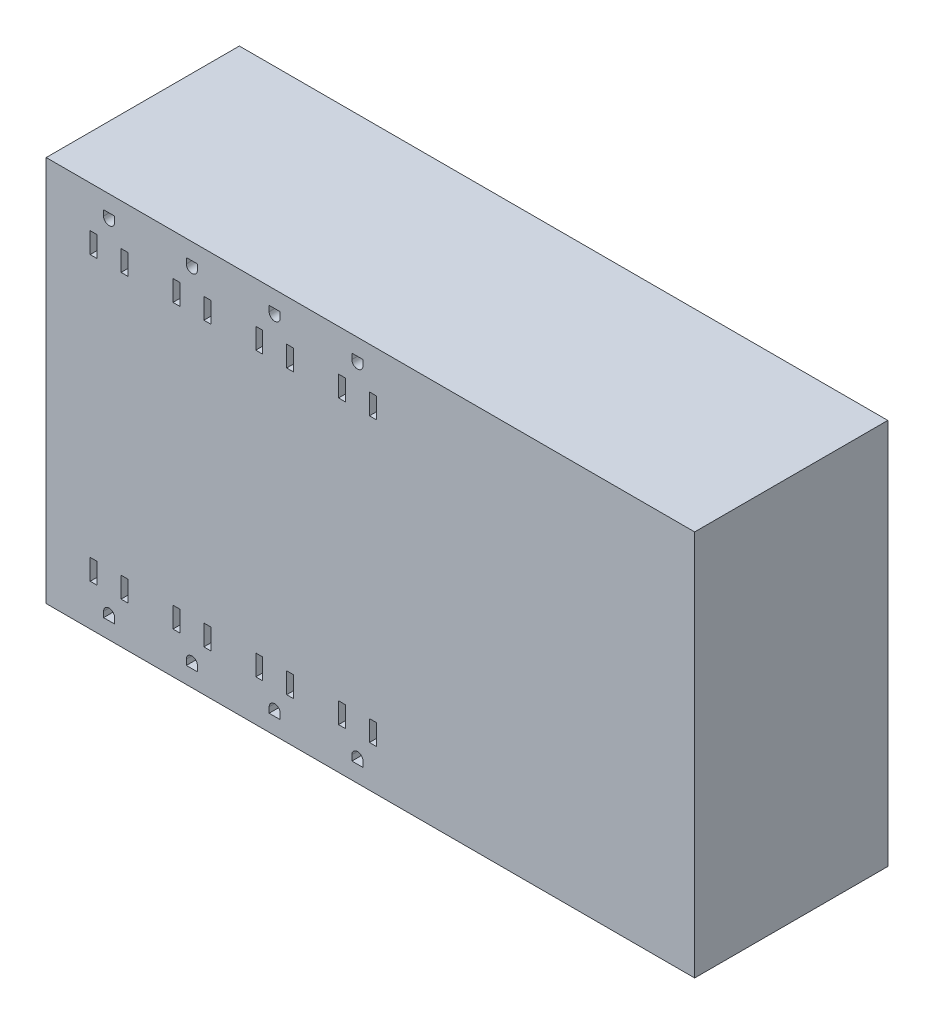
SolidWorks part; units mm, degrees
ref_plane "Front Plane" through (0, 0, 0) normal (0, 0, 1) x (1, 0, 0)
ref_plane "Top Plane" through (0, 0, 0) normal (0, 1, 0) x (1, 0, 0)
ref_plane "Right Plane" through (0, 0, 0) normal (1, 0, 0) x (0, 0, -1)
sketch "Sketch1" plane through (0, 0, 0) normal (0, 0, 1) x (1, 0, 0)
  line L1 (-149.225, -88.9) -> (149.225, -88.9)
  line L2 (-149.225, -88.9) -> (-149.225, 88.9)
  line L3 (-149.225, 88.9) -> (149.225, 88.9)
  line L4 (149.225, -88.9) -> (149.225, 88.9)
  line L5 (-149.225, -88.9) -> (149.225, 88.9) construction
  line L6 (-149.225, 88.9) -> (149.225, -88.9) construction
  point P0 (0, 0)
extrude "Boss-Extrude1" add sketch "Sketch1" along normal blind 88.9
sketch "Sketch2" plane through (0, 0, 88.9) normal (0, 0, 1) x (1, 0, 0)
  line L1 (-111.5717, 60.3403) -> (-114.7467, 60.3403)
  line L2 (-125.7957, 60.3403) -> (-128.9707, 60.3403)
  line L3 (-125.7957, 60.3403) -> (-125.7957, 69.8653)
  line L4 (-125.7957, 69.8653) -> (-128.9707, 69.8653)
  line L5 (-128.9707, 60.3403) -> (-128.9707, 69.8653)
  line L6 (-111.5717, 60.3403) -> (-111.5717, 69.8653)
  line L7 (-111.5717, 69.8653) -> (-114.7467, 69.8653)
  line L8 (-114.7467, 60.3403) -> (-114.7467, 69.8653)
  line L9 (-73.4717, 60.3403) -> (-76.6467, 60.3403)
  line L10 (-87.6957, 60.3403) -> (-90.8707, 60.3403)
  line L11 (-87.6957, 60.3403) -> (-87.6957, 69.8653)
  line L12 (-122.8112, 81.2953) -> (-117.7312, 81.2953)
  line L13 (-122.8112, 81.2953) -> (-122.8112, 78.7553)
  line L14 (-87.6957, 69.8653) -> (-90.8707, 69.8653)
  line L15 (-117.7312, 81.2953) -> (-117.7312, 78.7553)
  line L16 (-90.8707, 60.3403) -> (-90.8707, 69.8653)
  line L17 (-73.4717, 60.3403) -> (-73.4717, 69.8653)
  line L18 (-73.4717, 69.8653) -> (-76.6467, 69.8653)
  line L19 (-76.6467, 60.3403) -> (-76.6467, 69.8653)
  line L20 (-84.7112, 81.2953) -> (-79.6312, 81.2953)
  line L21 (-84.7112, 81.2953) -> (-84.7112, 78.7553)
  line L22 (-79.6312, 81.2953) -> (-79.6312, 78.7553)
  line L23 (-35.3717, 60.3403) -> (-38.5467, 60.3403)
  line L24 (-49.5957, 60.3403) -> (-52.7707, 60.3403)
  line L25 (-49.5957, 60.3403) -> (-49.5957, 69.8653)
  line L26 (-49.5957, 69.8653) -> (-52.7707, 69.8653)
  line L27 (-52.7707, 60.3403) -> (-52.7707, 69.8653)
  line L28 (-35.3717, 60.3403) -> (-35.3717, 69.8653)
  line L29 (-35.3717, 69.8653) -> (-38.5467, 69.8653)
  line L30 (-38.5467, 60.3403) -> (-38.5467, 69.8653)
  line L31 (-46.6112, 81.2953) -> (-41.5312, 81.2953)
  line L32 (-46.6112, 81.2953) -> (-46.6112, 78.7553)
  line L33 (-41.5312, 81.2953) -> (-41.5312, 78.7553)
  line L34 (2.7283, 60.3403) -> (-0.4467, 60.3403)
  line L35 (-11.4957, 60.3403) -> (-14.6707, 60.3403)
  line L36 (-11.4957, 60.3403) -> (-11.4957, 69.8653)
  line L37 (-11.4957, 69.8653) -> (-14.6707, 69.8653)
  line L38 (-14.6707, 60.3403) -> (-14.6707, 69.8653)
  line L39 (2.7283, 60.3403) -> (2.7283, 69.8653)
  line L40 (2.7283, 69.8653) -> (-0.4467, 69.8653)
  line L41 (-0.4467, 60.3403) -> (-0.4467, 69.8653)
  line L42 (-8.5112, 81.2953) -> (-3.4312, 81.2953)
  line L43 (-8.5112, 81.2953) -> (-8.5112, 78.7553)
  line L44 (-3.4312, 81.2953) -> (-3.4312, 78.7553)
  line L45 (-3.4312, -81.2953) -> (-3.4312, -78.7553)
  line L46 (-8.5112, -81.2953) -> (-8.5112, -78.7553)
  line L47 (-8.5112, -81.2953) -> (-3.4312, -81.2953)
  line L48 (-0.4467, -60.3403) -> (-0.4467, -69.8653)
  line L49 (2.7283, -69.8653) -> (-0.4467, -69.8653)
  line L50 (2.7283, -60.3403) -> (2.7283, -69.8653)
  line L51 (-14.6707, -60.3403) -> (-14.6707, -69.8653)
  line L52 (-11.4957, -69.8653) -> (-14.6707, -69.8653)
  line L53 (-11.4957, -60.3403) -> (-11.4957, -69.8653)
  line L54 (-11.4957, -60.3403) -> (-14.6707, -60.3403)
  line L55 (2.7283, -60.3403) -> (-0.4467, -60.3403)
  line L56 (-41.5312, -81.2953) -> (-41.5312, -78.7553)
  line L57 (-46.6112, -81.2953) -> (-46.6112, -78.7553)
  line L58 (-46.6112, -81.2953) -> (-41.5312, -81.2953)
  line L59 (-38.5467, -60.3403) -> (-38.5467, -69.8653)
  line L60 (-35.3717, -69.8653) -> (-38.5467, -69.8653)
  line L61 (-35.3717, -60.3403) -> (-35.3717, -69.8653)
  line L62 (-52.7707, -60.3403) -> (-52.7707, -69.8653)
  line L63 (-49.5957, -69.8653) -> (-52.7707, -69.8653)
  line L64 (-49.5957, -60.3403) -> (-49.5957, -69.8653)
  line L65 (-49.5957, -60.3403) -> (-52.7707, -60.3403)
  line L66 (-35.3717, -60.3403) -> (-38.5467, -60.3403)
  line L67 (-79.6312, -81.2953) -> (-79.6312, -78.7553)
  line L68 (-84.7112, -81.2953) -> (-84.7112, -78.7553)
  line L69 (-84.7112, -81.2953) -> (-79.6312, -81.2953)
  line L70 (-76.6467, -60.3403) -> (-76.6467, -69.8653)
  line L71 (-73.4717, -69.8653) -> (-76.6467, -69.8653)
  line L72 (-73.4717, -60.3403) -> (-73.4717, -69.8653)
  line L73 (-90.8707, -60.3403) -> (-90.8707, -69.8653)
  line L74 (-117.7312, -81.2953) -> (-117.7312, -78.7553)
  line L75 (-87.6957, -69.8653) -> (-90.8707, -69.8653)
  line L76 (-122.8112, -81.2953) -> (-122.8112, -78.7553)
  line L77 (-122.8112, -81.2953) -> (-117.7312, -81.2953)
  line L78 (-87.6957, -60.3403) -> (-87.6957, -69.8653)
  line L79 (-87.6957, -60.3403) -> (-90.8707, -60.3403)
  line L80 (-73.4717, -60.3403) -> (-76.6467, -60.3403)
  line L81 (-114.7467, -60.3403) -> (-114.7467, -69.8653)
  line L82 (-111.5717, -69.8653) -> (-114.7467, -69.8653)
  line L83 (-111.5717, -60.3403) -> (-111.5717, -69.8653)
  line L84 (-128.9707, -60.3403) -> (-128.9707, -69.8653)
  line L85 (-125.7957, -69.8653) -> (-128.9707, -69.8653)
  line L86 (-125.7957, -60.3403) -> (-125.7957, -69.8653)
  line L87 (-125.7957, -60.3403) -> (-128.9707, -60.3403)
  line L88 (-111.5717, -60.3403) -> (-114.7467, -60.3403)
  arc A0 (-122.8112, 78.7553) -> (-117.7312, 78.7553) centre (-120.2712, 78.7553) ccw
  arc A1 (-84.7112, 78.7553) -> (-79.6312, 78.7553) centre (-82.1712, 78.7553) ccw
  arc A2 (-46.6112, 78.7553) -> (-41.5312, 78.7553) centre (-44.0712, 78.7553) ccw
  arc A3 (-8.5112, 78.7553) -> (-3.4312, 78.7553) centre (-5.9712, 78.7553) ccw
  arc A4 (-8.5112, -78.7553) -> (-3.4312, -78.7553) centre (-5.9712, -78.7553) cw
  arc A5 (-46.6112, -78.7553) -> (-41.5312, -78.7553) centre (-44.0712, -78.7553) cw
  arc A6 (-84.7112, -78.7553) -> (-79.6312, -78.7553) centre (-82.1712, -78.7553) cw
  arc A7 (-122.8112, -78.7553) -> (-117.7312, -78.7553) centre (-120.2712, -78.7553) cw
  dimension "D1" = 2
  dimension "D2" = 4
extrude "Cut-Extrude1" cut sketch "Sketch2" against normal blind 12.7
